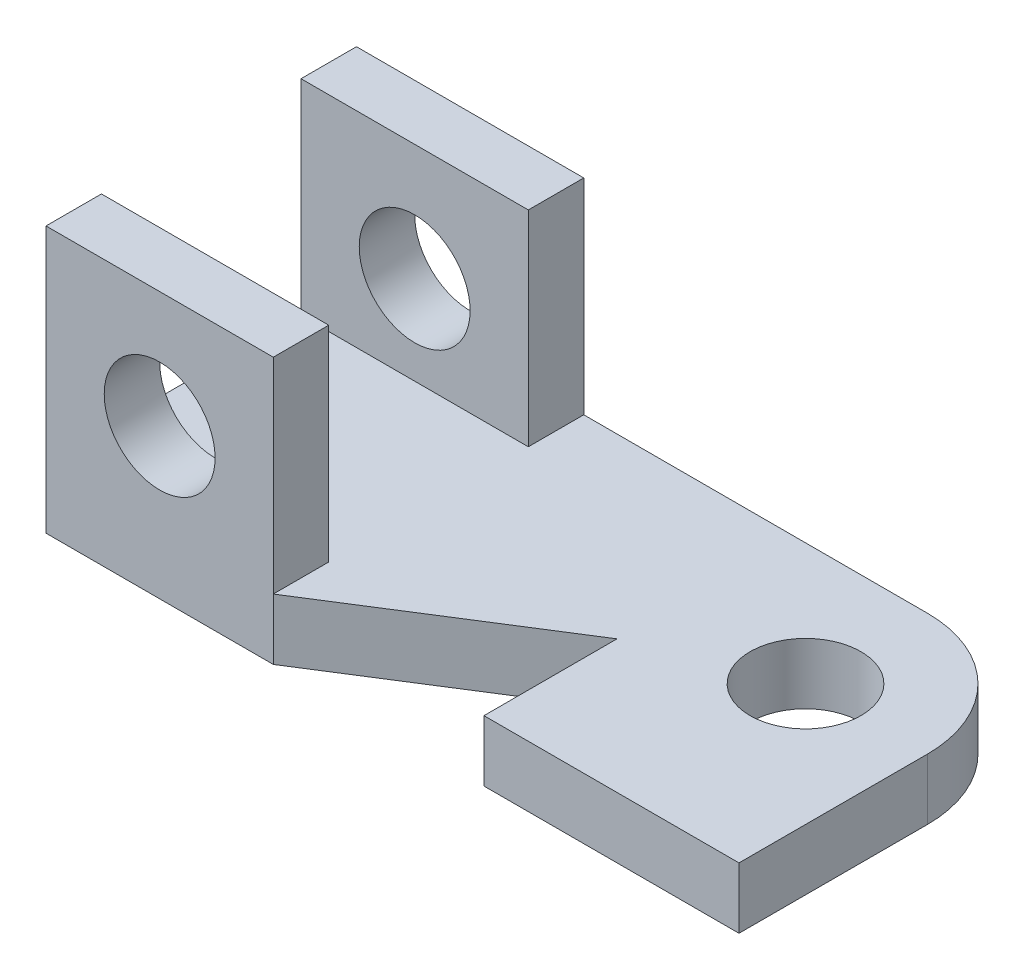
SolidWorks part; units mm, degrees
material "1060 Alloy"
ref_plane "Front Plane" through (0, 0, 0) normal (0, 0, 1) x (1, 0, 0)
ref_plane "Top Plane" through (0, 0, 0) normal (0, 1, 0) x (1, 0, 0)
ref_plane "Right Plane" through (0, 0, 0) normal (1, 0, 0) x (0, 0, -1)
sketch "Sketch2" plane through (0, 0, 0) normal (0, 1, 0) x (1, 0, 0)
  line L0 (-46, 0) -> (-46, 24)
  line L1 (0, 0) -> (-46, 0)
  line L2 (0, 0) -> (0, 34)
  line L3 (-22, 56) -> (-125, 56)
  line L4 (-125, 0) -> (-125, 56)
  line L5 (-84, 0) -> (-46, 24)
  line L6 (-84, 0) -> (-125, 0)
  arc A0 (0, 34) -> (-22, 56) centre (-22, 34) ccw
  circle A1 centre (-22, 34) radius 10
  point P5 (-84, 0)
  point P6 (-46, 0)
  dimension "D6" = 22
  dimension "D7" = 20
  dimension "D1" = 125
  dimension "D2" = 56
  dimension "D3" = 41
  dimension "D4" = 38
  dimension "D5" = 24
extrude "Boss-Extrude1" add sketch "Sketch2" along normal blind 11
sketch "Sketch5" plane through (0, 11, 0) normal (0, 1, 0) x (1, 0, 0)
  line L1 (-125, 56) -> (-84, 56)
  line L2 (-125, 56) -> (-125, 46)
  line L3 (-125, 46) -> (-84, 46)
  line L4 (-84, 56) -> (-84, 46)
  line L5 (-125, 0) -> (-84, 0)
  line L6 (-125, 0) -> (-125, 10)
  line L7 (-125, 10) -> (-84, 10)
  line L8 (-84, 0) -> (-84, 10)
  dimension "D1" = 10
  dimension "D2" = 41
  dimension "D3" = 10
  dimension "D4" = 41
extrude "Boss-Extrude3" add sketch "Sketch5" along normal blind 37
sketch "Sketch6" plane through (0, 0, 0) normal (0, 0, 1) x (1, 0, 0)
  line L0 (-125, 48) -> (-125, 0) construction
  line L2 (-125, 0) -> (-84, 0) construction
  circle A0 centre (-104.5, 27) radius 10
  dimension "D1" = 20
  dimension "D2" = 20.5
  dimension "D3" = 27
extrude "Cut-Extrude1" cut sketch "Sketch6" against normal through all and the other way through all
